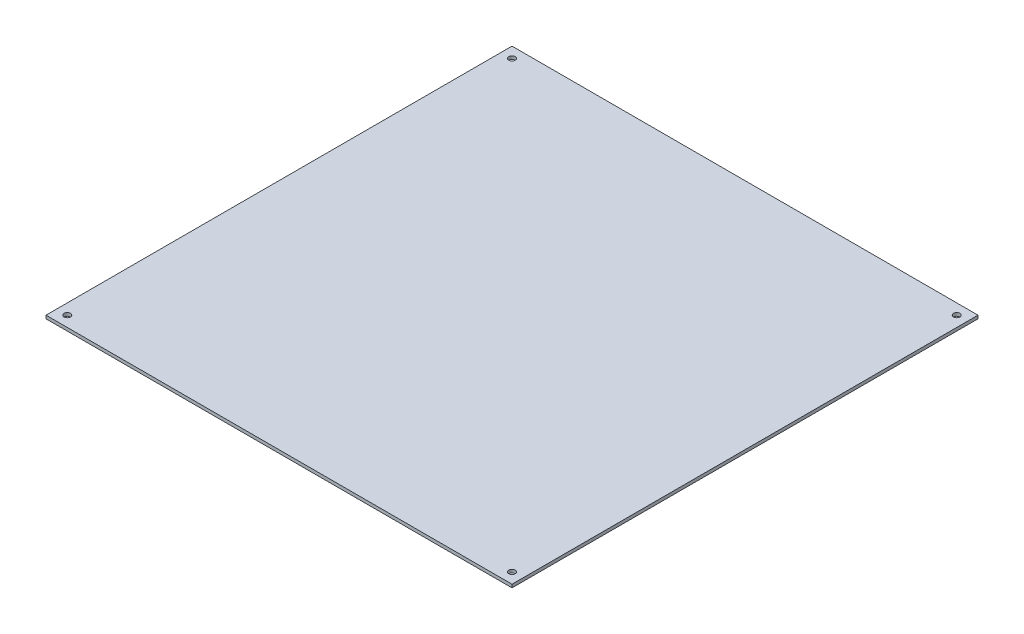
SolidWorks part; units mm, degrees
ref_plane "Front Plane" through (0, 0, 0) normal (0, 0, 1) x (1, 0, 0)
ref_plane "Top Plane" through (0, 0, 0) normal (0, 1, 0) x (1, 0, 0)
ref_plane "Right Plane" through (0, 0, 0) normal (1, 0, 0) x (0, 0, -1)
sketch "Sketch1" plane through (0, 0, 0) normal (0, 1, 0) x (1, 0, 0)
  line L0 (-214, 214) -> (-5, 214) construction
  line L1 (-219, 219) -> (0, 219)
  line L2 (-219, 219) -> (-219, 0)
  line L3 (-219, 0) -> (0, 0)
  line L4 (0, 219) -> (0, 0)
  line L5 (-5, 214) -> (-5, 5) construction
  line L6 (-5, 5) -> (-214, 5) construction
  line L7 (-214, 5) -> (-214, 214) construction
  circle A0 centre (-214, 214) radius 1.5
  circle A1 centre (-214, 5) radius 1.5
  circle A2 centre (-5, 5) radius 1.5
  circle A3 centre (-5, 214) radius 1.5
  dimension "D6" = 3
  dimension "D7" = 5
  dimension "D1" = 219
  dimension "D2" = 219
  dimension "D3" = 209
  dimension "D4" = 209
  dimension "D5" = 5
extrude "Boss-Extrude1" add sketch "Sketch1" along normal blind 1.5
